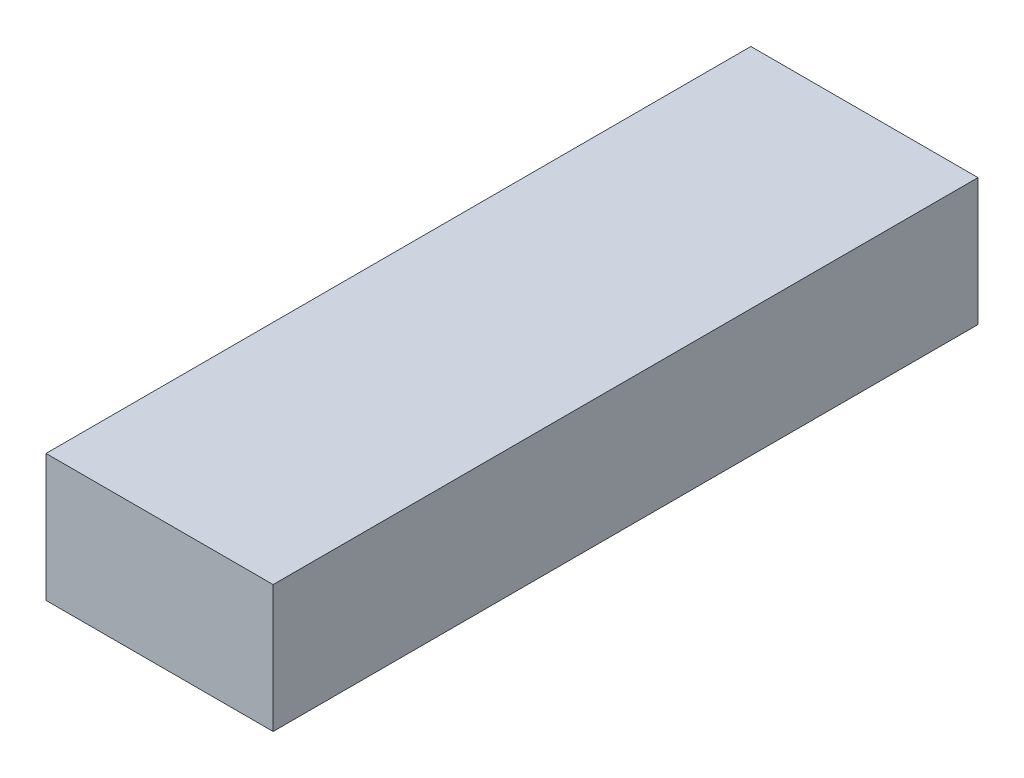
SolidWorks part; units mm, degrees
ref_plane "Front Plane" through (0, 0, 0) normal (0, 0, 1) x (1, 0, 0)
ref_plane "Top Plane" through (0, 0, 0) normal (0, 1, 0) x (1, 0, 0)
ref_plane "Right Plane" through (0, 0, 0) normal (1, 0, 0) x (0, 0, -1)
sketch "Sketch3" plane through (0, 0, 0) normal (0, 1, 0) x (1, 0, 0)
  line L1 (-17.4, -54) -> (17.4, -54)
  line L2 (-17.4, -54) -> (-17.4, 54)
  line L3 (-17.4, 54) -> (17.4, 54)
  line L4 (17.4, -54) -> (17.4, 54)
  point P4 (0, -54)
  point P5 (-17.4, 0)
  dimension "D1" = 108
  dimension "D2" = 34.8
extrude "Boss-Extrude1" add sketch "Sketch3" along normal blind 19.5
